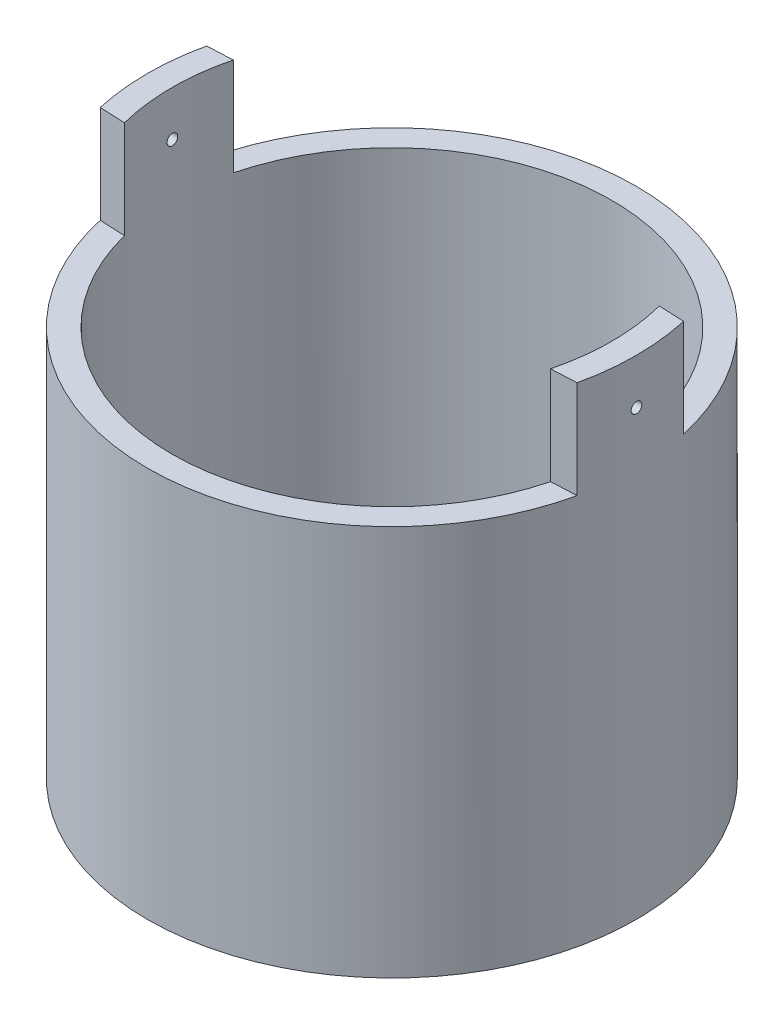
SolidWorks part; units mm, degrees
ref_plane "Front Plane" through (0, 0, 0) normal (0, 0, 1) x (1, 0, 0)
ref_plane "Top Plane" through (0, 0, 0) normal (0, 1, 0) x (1, 0, 0)
ref_plane "Right Plane" through (0, 0, 0) normal (1, 0, 0) x (0, 0, -1)
sketch "Sketch1" plane through (0, 0, 0) normal (0, 1, 0) x (1, 0, 0)
  circle A0 centre (0, 0) radius 63.5
  dimension "D1" = 127
extrude "Boss-Extrude1" add sketch "Sketch1" along normal blind 76.2
sketch "Sketch2" plane through (0, 76.2, 0) normal (0, 1, 0) x (1, 0, 0)
  circle A0 centre (0, 0) radius 57.15
extrude "Cut-Extrude1" cut sketch "Sketch2" against normal blind 69.85
sketch "Sketch4" plane through (0, 0, 0) normal (0, -1, 0) x (1, 0, 0)
  circle A0 centre (0, 0) radius 25.4
  dimension "D1" = 50.8
extrude "Boss-Extrude2" add sketch "Sketch4" along normal blind 25.4
sketch "Sketch5" plane through (0, -25.4, 0) normal (0, -1, 0) x (1, 0, 0)
  circle A0 centre (0, 0) radius 22.225
  dimension "D1" = 44.45
extrude "Cut-Extrude2" cut sketch "Sketch5" against normal blind 2514.6
sketch "Sketch8" plane through (0, 76.2, 0) normal (0, 1, 0) x (1, 0, 0)
  circle A0 centre (0, 0) radius 63.5
  dimension "D1" = 127
extrude "Boss-Extrude3" add sketch "Sketch8" along normal blind 25.4
sketch "Sketch9" plane through (0, 101.6, 0) normal (0, 1, 0) x (1, 0, 0)
  circle A0 centre (0, 0) radius 57.15
  dimension "D1" = 114.3
extrude "Cut-Extrude3" cut sketch "Sketch9" against normal blind 50.8
sketch "Sketch11" plane through (0, 101.6, 0) normal (0, 1, 0) x (1, 0, 0)
  line L0 (-61.976, 13.8284) -> (-55.372, 14.1444)
  line L1 (-61.976, -13.8284) -> (-55.372, -14.1444)
  arc A0 (-61.976, 13.8284) -> (-61.976, -13.8284) centre (0, 0) ccw
  circle A1 centre (0, 0) radius 63.5 construction
  arc A2 (-55.372, 14.1444) -> (-55.372, -14.1444) centre (0, 0) ccw
  circle A3 centre (0, 0) radius 57.15 construction
  dimension "D1" = 61.976
  dimension "D2" = 61.976
  dimension "D3" = 55.372
  dimension "D4" = 55.372
sketch "Sketch12" plane through (0, 101.6, 0) normal (0, 1, 0) x (1, 0, 0)
  line L0 (0, 63.5) -> (0, -63.5) construction
  circle A0 centre (0, 0) radius 63.5 construction
sketch "Sketch13" plane through (0, 101.6, 0) normal (0, 1, 0) x (1, 0, 0)
  line L0 (55.372, 14.1444) -> (61.976, 13.8284)
  line L1 (55.372, -14.1444) -> (61.976, -13.8284)
  arc A0 (61.976, 13.8284) -> (61.976, -13.8284) centre (0, 0) cw
  circle A1 centre (0, 0) radius 63.5 construction
  arc A2 (55.372, 14.1444) -> (55.372, -14.1444) centre (0, 0) cw
  circle A3 centre (0, 0) radius 57.15 construction
  dimension "D1" = 61.976
  dimension "D2" = 61.976
  dimension "D3" = 55.372
  dimension "D4" = 55.372
extrude "Boss-Extrude5" add sketch "Sketch11" along normal blind 25.4
extrude "Boss-Extrude6" add sketch "Sketch13" along normal blind 25.4
ref_plane "Plane1" through (101.6, 0, 0) normal (1, 0, 0) x (0, 0, -1)
sketch "Sketch14" plane through (101.6, 0, 0) normal (1, 0, 0) x (0, 0, -1)
  line L0 (13.8284, 127) -> (-13.8284, 127) construction
  circle A0 centre (0.0817, 115.2193) radius 1.3891
  dimension "D1" = 2.7781
  dimension "D2" = 11.7807
  dimension "D3" = 65.024
extrude "Cut-Extrude4" cut sketch "Sketch14" against normal blind 2514.6
